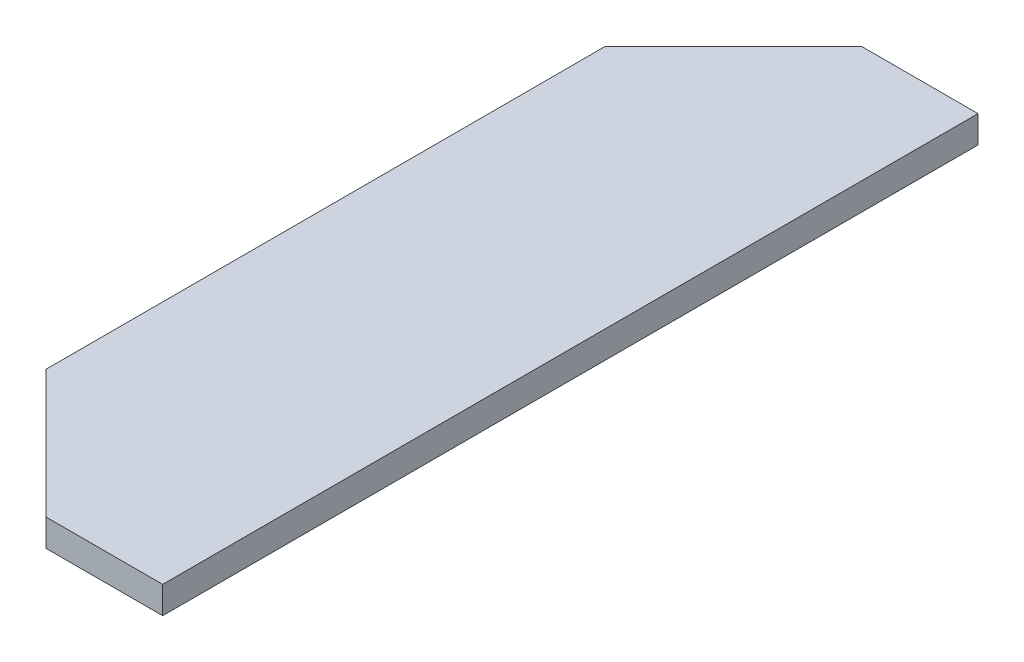
SolidWorks part; units mm, degrees
ref_plane "Front Plane" through (0, 0, 0) normal (0, 0, 1) x (1, 0, 0)
ref_plane "Top Plane" through (0, 0, 0) normal (0, 1, 0) x (1, 0, 0)
ref_plane "Right Plane" through (0, 0, 0) normal (1, 0, 0) x (0, 0, -1)
sketch "Sketch1" plane through (0, 0, 0) normal (0, 1, 0) x (1, 0, 0)
  line L0 (45, 150) -> (2.0711, 150)
  line L1 (2.0711, 150) -> (-45, 102.9289)
  line L2 (-45, 102.9289) -> (-45, -102.9289)
  line L3 (-45, -102.9289) -> (2.0711, -150)
  line L4 (2.0711, -150) -> (45, -150)
  line L5 (45, -150) -> (45, 150)
extrude "Boss-Extrude1" add sketch "Sketch1" along normal blind 10
